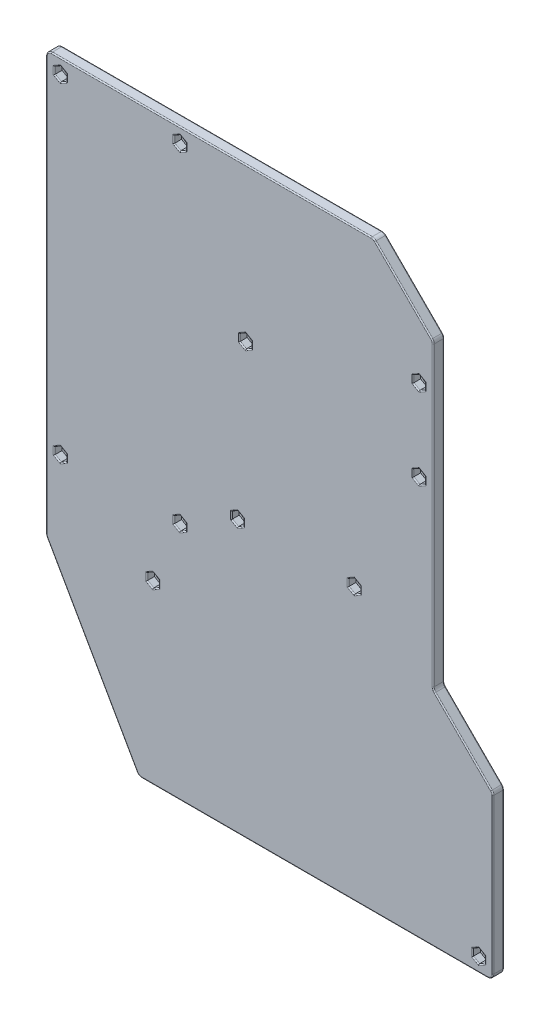
SolidWorks part; units mm, degrees
ref_plane "Front Plane" through (0, 0, 0) normal (0, 0, 1) x (1, 0, 0)
ref_plane "Top Plane" through (0, 0, 0) normal (0, 1, 0) x (1, 0, 0)
ref_plane "Right Plane" through (0, 0, 0) normal (1, 0, 0) x (0, 0, -1)
sketch "Sketch1" plane through (0, 0, 0) normal (0, 0, 1) x (1, 0, 0)
  line L4 (59.9, 218.7) -> (32.8, 245.8)
  line L6 (59.9, 54.65) -> (59.9, 245.8) construction
  line L11 (-115.9756, 227.8) -> (-115.9756, 239.3) construction
  line L13 (-115.9756, 245.8) -> (-115.9756, 54.65)
  line L14 (-115.9756, 54.65) -> (59.9, 54.65) construction
  line L16 (-60.5, 54.65) -> (73.5, 54.65) construction
  line L17 (80.5, -19.15) -> (-73.5, -19.15) construction
  line L18 (87, -19.15) -> (-74, -19.15)
  line L19 (87, -19.15) -> (87, 54.65)
  line L20 (87, 54.65) -> (-74, 54.65) construction
  line L21 (-74, -19.15) -> (-74, 54.65) construction
  line L22 (-74, -18.65) -> (-74, 61.15) construction
  line L23 (-74, -19.15) -> (-115.9756, 54.65)
  line L24 (87, 54.65) -> (59.9, 81.75)
  line L26 (-115.9756, 245.8) -> (32.8, 245.8)
  line L28 (59.9, 218.7) -> (59.9, 81.75)
  line L30 (59.9, 245.8) -> (32.8, 245.8) construction
  circle A0 centre (53.4, 162.35) radius 1.5 construction
  circle A1 centre (53.4, 199.35) radius 1.5 construction
  circle A2 centre (-25.4, 176.25) radius 1.5 construction
  circle A3 centre (-29, 104.55) radius 1.5 construction
  circle A4 centre (24, 104.55) radius 1.5 construction
  circle A5 centre (80.5, -12.65) radius 1.5 construction
  circle A6 centre (-67.5, 61.15) radius 1.5 construction
  circle A7 centre (-109.4756, 89.7) radius 1.5 construction
  circle A8 centre (-55.2, 89.7) radius 1.5 construction
  circle A9 centre (-55.2, 239.3) radius 1.5 construction
  circle A10 centre (-109.4756, 239.3) radius 1.5 construction
  circle A11 centre (53.4, 162.35) radius 1.5
  circle A12 centre (53.4, 199.35) radius 1.5
  circle A13 centre (-25.4, 176.25) radius 1.5
  circle A14 centre (-29, 104.55) radius 1.5
  circle A15 centre (24, 104.55) radius 1.5
  circle A16 centre (80.5, -12.65) radius 1.5
  circle A17 centre (-67.5, 61.15) radius 1.5
  circle A18 centre (-109.4756, 89.7) radius 1.5
  circle A19 centre (-55.2, 89.7) radius 1.5
  circle A20 centre (-55.2, 239.3) radius 1.5
  circle A21 centre (-109.4756, 239.3) radius 1.5
  arc A25 (53.4, 192.85) -> (53.4, 205.85) centre (53.4, 199.35) ccw construction
  arc A26 (-102.9756, 239.3) -> (-115.9756, 239.3) centre (-109.4756, 239.3) ccw construction
  arc A35 (80.5, -19.15) -> (80.5, -6.15) centre (80.5, -12.65) ccw construction
  point P36 (59.9, 221.7433)
  dimension "D1" = 45
  dimension "D2" = 45
extrude "Boss-Extrude1" add sketch "Sketch1" along normal blind 1.5
sketch "Sketch2" plane through (0, 0, 1.5) normal (0, 0, 1) x (1, 0, 0)
  line L0 (-115.9756, 245.8) -> (-115.9756, 54.65) construction
  line L1 (-109.4756, 242.4754) -> (-112.2256, 240.8877)
  line L2 (-112.2256, 240.8877) -> (-112.2256, 237.7123)
  line L3 (-112.2256, 237.7123) -> (-109.4756, 236.1246)
  line L4 (-109.4756, 236.1246) -> (-106.7256, 237.7123)
  line L5 (-106.7256, 237.7123) -> (-106.7256, 240.8877)
  line L6 (-106.7256, 240.8877) -> (-109.4756, 242.4754)
  line L7 (-55.2, 242.4754) -> (-57.95, 240.8877)
  line L8 (-57.95, 240.8877) -> (-57.95, 237.7123)
  line L9 (-57.95, 237.7123) -> (-55.2, 236.1246)
  line L10 (-55.2, 236.1246) -> (-52.45, 237.7123)
  line L11 (-52.45, 237.7123) -> (-52.45, 240.8877)
  line L12 (-52.45, 240.8877) -> (-55.2, 242.4754)
  line L13 (-25.4, 179.4254) -> (-28.15, 177.8377)
  line L14 (-28.15, 177.8377) -> (-28.15, 174.6623)
  line L15 (-28.15, 174.6623) -> (-25.4, 173.0746)
  line L16 (-25.4, 173.0746) -> (-22.65, 174.6623)
  line L17 (-22.65, 174.6623) -> (-22.65, 177.8377)
  line L18 (-22.65, 177.8377) -> (-25.4, 179.4254)
  line L19 (53.4, 202.5254) -> (50.65, 200.9377)
  line L20 (50.65, 200.9377) -> (50.65, 197.7623)
  line L21 (50.65, 197.7623) -> (53.4, 196.1746)
  line L22 (53.4, 196.1746) -> (56.15, 197.7623)
  line L23 (56.15, 197.7623) -> (56.15, 200.9377)
  line L24 (56.15, 200.9377) -> (53.4, 202.5254)
  line L25 (53.4, 165.5254) -> (50.65, 163.9377)
  line L26 (50.65, 163.9377) -> (50.65, 160.7623)
  line L27 (50.65, 160.7623) -> (53.4, 159.1746)
  line L28 (53.4, 159.1746) -> (56.15, 160.7623)
  line L29 (56.15, 160.7623) -> (56.15, 163.9377)
  line L30 (56.15, 163.9377) -> (53.4, 165.5254)
  line L31 (24, 107.7254) -> (21.25, 106.1377)
  line L32 (21.25, 106.1377) -> (21.25, 102.9623)
  line L33 (21.25, 102.9623) -> (24, 101.3746)
  line L34 (24, 101.3746) -> (26.75, 102.9623)
  line L35 (26.75, 102.9623) -> (26.75, 106.1377)
  line L36 (26.75, 106.1377) -> (24, 107.7254)
  line L37 (-29, 107.7254) -> (-31.75, 106.1377)
  line L38 (-31.75, 106.1377) -> (-31.75, 102.9623)
  line L39 (-31.75, 102.9623) -> (-29, 101.3746)
  line L40 (-29, 101.3746) -> (-26.25, 102.9623)
  line L41 (-26.25, 102.9623) -> (-26.25, 106.1377)
  line L42 (-26.25, 106.1377) -> (-29, 107.7254)
  line L43 (-55.2, 92.8754) -> (-57.95, 91.2877)
  line L44 (-57.95, 91.2877) -> (-57.95, 88.1123)
  line L45 (-57.95, 88.1123) -> (-55.2, 86.5246)
  line L46 (-55.2, 86.5246) -> (-52.45, 88.1123)
  line L47 (-52.45, 88.1123) -> (-52.45, 91.2877)
  line L48 (-52.45, 91.2877) -> (-55.2, 92.8754)
  line L49 (-109.4756, 92.8754) -> (-112.2256, 91.2877)
  line L50 (-112.2256, 91.2877) -> (-112.2256, 88.1123)
  line L51 (-112.2256, 88.1123) -> (-109.4756, 86.5246)
  line L52 (-109.4756, 86.5246) -> (-106.7256, 88.1123)
  line L53 (-106.7256, 88.1123) -> (-106.7256, 91.2877)
  line L54 (-106.7256, 91.2877) -> (-109.4756, 92.8754)
  line L55 (-67.5, 64.3254) -> (-70.25, 62.7377)
  line L56 (-70.25, 62.7377) -> (-70.25, 59.5623)
  line L57 (-70.25, 59.5623) -> (-67.5, 57.9746)
  line L58 (-67.5, 57.9746) -> (-64.75, 59.5623)
  line L59 (-64.75, 59.5623) -> (-64.75, 62.7377)
  line L60 (-64.75, 62.7377) -> (-67.5, 64.3254)
  line L61 (80.5, -9.4746) -> (77.75, -11.0623)
  line L62 (77.75, -11.0623) -> (77.75, -14.2377)
  line L63 (77.75, -14.2377) -> (80.5, -15.8254)
  line L64 (80.5, -15.8254) -> (83.25, -14.2377)
  line L65 (83.25, -14.2377) -> (83.25, -11.0623)
  line L66 (83.25, -11.0623) -> (80.5, -9.4746)
  line L67 (-74, -19.15) -> (-115.9756, 54.65) construction
  line L68 (87, -19.15) -> (-74, -19.15) construction
  line L69 (87, -19.15) -> (87, 54.65) construction
  line L70 (87, 54.65) -> (59.9, 81.75) construction
  line L71 (59.9, 218.7) -> (59.9, 81.75) construction
  line L73 (-115.9756, 245.8) -> (32.8, 245.8) construction
  line L74 (-115.9756, 245.8) -> (-115.9756, 54.65)
  line L75 (-74, -19.15) -> (-115.9756, 54.65)
  line L76 (87, -19.15) -> (-74, -19.15)
  line L77 (87, -19.15) -> (87, 54.65)
  line L78 (87, 54.65) -> (59.9, 81.75)
  line L79 (59.9, 218.7) -> (59.9, 81.75)
  line L81 (-115.9756, 245.8) -> (32.8, 245.8)
  line L82 (59.9, 218.7) -> (32.8, 245.8) construction
  line L83 (59.9, 218.7) -> (32.8, 245.8)
  circle A0 centre (-109.4756, 239.3) radius 2.75 construction
  circle A1 centre (-55.2, 239.3) radius 2.75 construction
  circle A2 centre (-25.4, 176.25) radius 2.75 construction
  circle A3 centre (53.4, 199.35) radius 2.75 construction
  circle A4 centre (53.4, 162.35) radius 2.75 construction
  circle A5 centre (24, 104.55) radius 2.75 construction
  circle A6 centre (-29, 104.55) radius 2.75 construction
  circle A7 centre (-55.2, 89.7) radius 2.75 construction
  circle A8 centre (-109.4756, 89.7) radius 2.75 construction
  circle A9 centre (-67.5, 61.15) radius 2.75 construction
  circle A10 centre (80.5, -12.65) radius 2.75 construction
  dimension "D1" = 5.5
extrude "Boss-Extrude2" add sketch "Sketch2" along normal blind 3.5
fillet "Fillet1" radius 2.5 8 edges at (59.9, 81.75, 2.5) (87, 54.65, 2.5) (87, -19.15, 2.5) (-74, -19.15, 2.5) (-115.9756, 54.65, 2.5) (-115.9756, 245.8, 2.5) (59.9, 218.7, 2.5) (32.8, 245.8, 2.5)
fillet "Fillet2" radius 0.5 120 edges at (79.125, -10.2684, 5) (77.75, -12.65, 5) (79.125, -15.0316, 5) (81.875, -15.0316, 5) (83.25, -12.65, 5) (81.875, -10.2684, 5) (-110.8506, 92.0816, 5) (-112.2256, 89.7, 5) (-110.8506, 87.3184, 5) (-108.1006, 87.3184, 5) (-106.7256, 89.7, 5) (-108.1006, 92.0816, 5) (-30.375, 106.9316, 5) (-31.75, 104.55, 5) (-30.375, 102.1684, 5) (-27.625, 102.1684, 5) (-26.25, 104.55, 5) (-27.625, 106.9316, 5) (52.025, 164.7316, 5) (50.65, 162.35, 5) (52.025, 159.9684, 5) (54.775, 159.9684, 5) (56.15, 162.35, 5) (54.775, 164.7316, 5) (-26.775, 178.6316, 5) (-28.15, 176.25, 5) (-26.775, 173.8684, 5) (-24.025, 173.8684, 5) (-22.65, 176.25, 5) (-24.025, 178.6316, 5) (-110.8506, 241.6816, 5) (-112.2256, 239.3, 5) (-110.8506, 236.9184, 5) (-108.1006, 236.9184, 5) (-106.7256, 239.3, 5) (-108.1006, 241.6816, 5) (86.2678, -18.4178, 5) (5.9771, -19.15, 5) (-73.8028, -18.811, 5) (-95.1838, 18.0946, 5) (-115.8925, 54.672, 5) (-115.9756, 149.3056, 5) (-115.2434, 245.0678, 5) (-40.8556, 245.8, 5) (59.9, 150.225, 5) (60.0903, 81.8288, 5) (73.45, 68.2, 5) (86.8097, 54.5712, 5) (87, 18.4822, 5) (-56.575, 241.6816, 5) (-57.95, 239.3, 5) (-56.575, 236.9184, 5) (-53.825, 236.9184, 5) (-52.45, 239.3, 5) (-53.825, 241.6816, 5) (52.025, 201.7316, 5) (50.65, 199.35, 5) (52.025, 196.9684, 5) (54.775, 196.9684, 5) (56.15, 199.35, 5) (54.775, 201.7316, 5) (22.625, 106.9316, 5) (21.25, 104.55, 5) (22.625, 102.1684, 5) (25.375, 102.1684, 5) (26.75, 104.55, 5) (25.375, 106.9316, 5) (-56.575, 92.0816, 5) (-57.95, 89.7, 5) (-56.575, 87.3184, 5) (-53.825, 87.3184, 5) (-52.45, 89.7, 5) (-53.825, 92.0816, 5) (-68.875, 63.5316, 5) (-70.25, 61.15, 5) (-68.875, 58.7684, 5) (-66.125, 58.7684, 5) (-64.75, 61.15, 5) (-66.125, 63.5316, 5) (-107.9756, 239.3, 0) (-53.7, 89.7, 0) (-66, 61.15, 0) (25.5, 104.55, 0) (-23.9, 176.25, 0) (54.9, 162.35, 0) (60.0903, 81.8288, 0) (59.9, 150.225, 0) (-40.8556, 245.8, 0) (-115.2434, 245.0678, 0) (-115.9756, 149.3056, 0) (-115.8925, 54.672, 0) (-95.1838, 18.0946, 0) (-73.8028, -18.811, 0) (5.9771, -19.15, 0) (86.2678, -18.4178, 0) (87, 18.4822, 0) (86.8097, 54.5712, 0) (73.45, 68.2, 0) (54.9, 199.35, 0) (-27.5, 104.55, 0) (82, -12.65, 0) (-107.9756, 89.7, 0) (-53.7, 239.3, 0) (-107.9756, 239.3, 1.5) (-53.7, 239.3, 1.5) (-23.9, 176.25, 1.5) (54.9, 199.35, 1.5) (54.9, 162.35, 1.5) (-27.5, 104.55, 1.5) (25.5, 104.55, 1.5) (82, -12.65, 1.5) (-53.7, 89.7, 1.5) (-66, 61.15, 1.5) (-107.9756, 89.7, 1.5) (46.35, 232.25, 0) (46.35, 232.25, 5) (32.7212, 245.6097, 5) (59.7097, 218.6212, 5) (32.7212, 245.6097, 0) (59.7097, 218.6212, 0)
